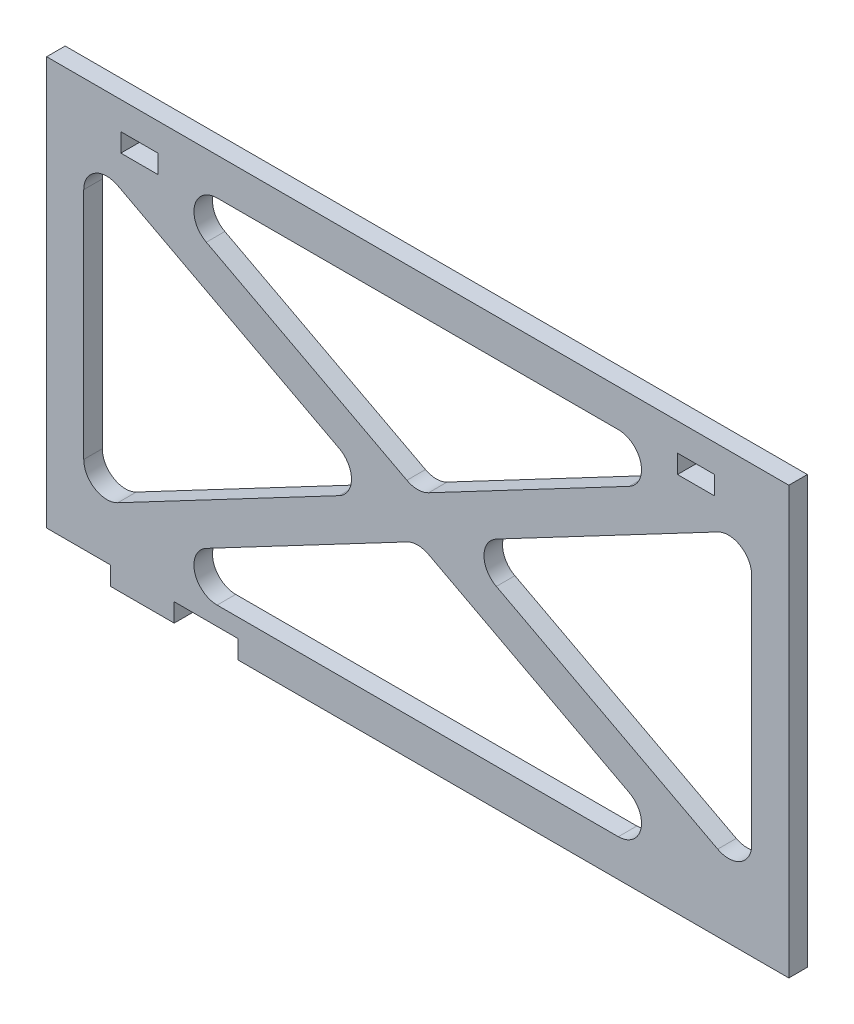
SolidWorks part; units mm, degrees
material "Beech"
ref_plane "Front Plane" through (0, 0, 0) normal (0, 0, 1) x (1, 0, 0)
ref_plane "Top Plane" through (0, 0, 0) normal (0, 1, 0) x (1, 0, 0)
ref_plane "Right Plane" through (0, 0, 0) normal (1, 0, 0) x (0, 0, -1)
sketch "Sketch1" plane through (0, 0, 0) normal (0, 0, 1) x (1, 0, 0)
  line L0 (91.44, 48.26) -> (-91.44, 48.26)
  line L1 (101.6, 58.42) -> (-101.6, 58.42)
  line L2 (101.6, 58.42) -> (101.6, -58.42)
  line L3 (101.6, -58.42) -> (-101.6, -58.42)
  line L4 (-101.6, 58.42) -> (-101.6, -58.42)
  line L5 (101.6, 58.42) -> (-101.6, -58.42) construction
  line L6 (101.6, -58.42) -> (-101.6, 58.42) construction
  line L7 (-91.44, 48.26) -> (-91.44, -48.26)
  line L8 (91.44, -48.26) -> (-91.44, -48.26)
  line L9 (91.44, 48.26) -> (91.44, -48.26)
  line L10 (-91.44, 48.26) -> (91.44, -48.26) construction
  line L11 (-91.44, -48.26) -> (91.44, 48.26) construction
  line L12 (-93.8111, 43.7673) -> (89.0689, -52.7527)
  line L13 (-89.0689, -52.7527) -> (93.8111, 43.7673)
  line L14 (-89.0689, 52.7527) -> (93.8111, -43.7673)
  line L15 (-93.8111, -43.7673) -> (89.0689, 52.7527)
  line L16 (0, 0) -> (0, 58.42) construction
  point P0 (0, 0)
  dimension "D1" = 116.84
  dimension "D2" = 203.2
  dimension "D3" = 10.16
  dimension "D4" = 5.08
  dimension "D5" = 5.08
extrude "Boss-Extrude1" add sketch "Sketch1" along normal blind 5.08
fillet "Fillet1" radius 6.35 12 edges at (10.8836, 0, 2.54) (91.44, -42.5159, 2.54) (80.5564, -48.26, 2.54) (-80.5564, -48.26, 2.54) (91.44, 42.5159, 2.54) (80.5564, 48.26, 2.54) (-80.5564, 48.26, 2.54) (0, -5.7441, 2.54) (-10.8836, 0, 2.54) (0, 5.7441, 2.54) (-91.44, -42.5159, 2.54) (-91.44, 42.5159, 2.54)
sketch "Sketch2" plane through (0, 0, 5.08) normal (0, 0, 1) x (1, 0, 0)
  line L0 (-81.28, 50.8) -> (-71.12, 50.8)
  line L1 (-81.28, 50.8) -> (-81.28, 45.72)
  line L2 (-81.28, 45.72) -> (-71.12, 45.72)
  line L3 (-71.12, 50.8) -> (-71.12, 45.72)
  line L4 (-81.28, 50.8) -> (-71.12, 45.72) construction
  line L5 (-81.28, 45.72) -> (-71.12, 50.8) construction
  line L6 (-101.6, 58.42) -> (-101.6, -58.42) construction
  line L7 (101.6, 58.42) -> (-101.6, 58.42) construction
  line L8 (0, 0) -> (0, 58.42) construction
  line L9 (81.28, 45.72) -> (71.12, 50.8) construction
  line L10 (81.28, 50.8) -> (71.12, 45.72) construction
  line L11 (71.12, 50.8) -> (71.12, 45.72)
  line L12 (81.28, 45.72) -> (71.12, 45.72)
  line L13 (81.28, 50.8) -> (81.28, 45.72)
  line L14 (81.28, 50.8) -> (71.12, 50.8)
  point P4 (-76.2, 48.26)
  point P16 (76.2, 48.26)
  dimension "D1" = 25.4
  dimension "D2" = 10.16
  dimension "D3" = 10.16
  dimension "D4" = 5.08
extrude "Cut-Extrude1" cut sketch "Sketch2" against normal through all both and the other way through all
sketch "Sketch3" plane through (0, 0, 5.08) normal (0, 0, 1) x (1, 0, 0)
  line L0 (0, 0) -> (0, -58.42)
  line L1 (101.6, -58.42) -> (-101.6, -58.42) construction
  line L2 (0, -58.42) -> (-101.6, -58.42)
  line L3 (-101.6, -53.34) -> (0, -53.34)
  line L4 (-101.6, 58.42) -> (-101.6, -58.42) construction
  line L5 (-84.1375, -53.34) -> (-84.1375, -58.42)
  line L6 (-101.6, -53.34) -> (-101.6, -58.42)
  line L7 (-66.675, -53.34) -> (-66.675, -58.42)
  line L8 (-49.2125, -53.34) -> (-49.2125, -58.42)
  line L9 (-31.75, -53.34) -> (-31.75, -58.42)
  line M36 (-101.6, 58.42) -> (-101.6, -58.42)
  line M37 (-101.6, -58.42) -> (101.6, -58.42)
  dimension "D1" = 5.08
  dimension "D2" = 17.4625
  dimension "D3" = 17.4625
  dimension "D4" = 17.4625
  dimension "D5" = 17.4625
extrude "Cut-Extrude2" cut sketch "Sketch3" against normal blind 10.16 contours L5 L3 M36 M37 | L8 L3 L7 M37
